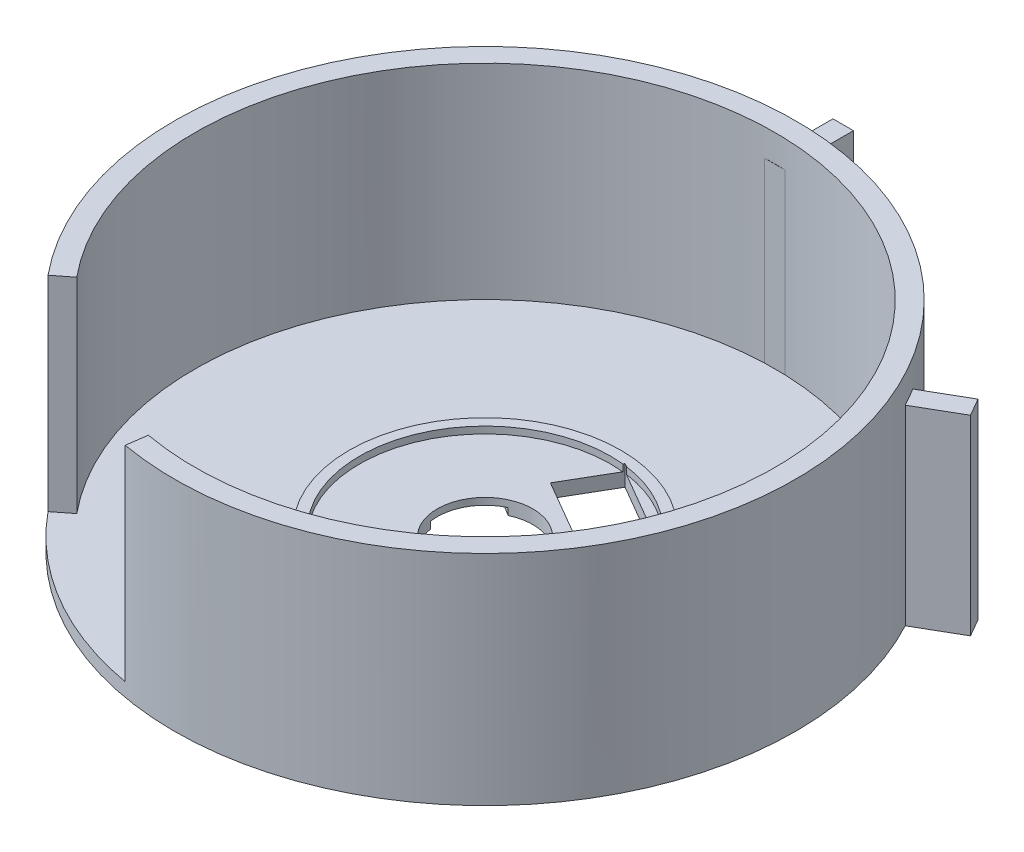
SolidWorks part; units mm, degrees
ref_plane "Front Plane" through (0, 0, 0) normal (0, 0, 1) x (1, 0, 0)
ref_plane "Top Plane" through (0, 0, 0) normal (0, 1, 0) x (1, 0, 0)
ref_plane "Right Plane" through (0, 0, 0) normal (1, 0, 0) x (0, 0, -1)
sketch "Sketch1" plane through (0, 0, 0) normal (0, 1, 0) x (1, 0, 0)
  circle A0 centre (0, 0) radius 45.5
  circle A1 centre (0, 0) radius 42.5
  dimension "D1" = 85
  dimension "D2" = 3
  dimension "D3" = 91
extrude "Boss-Extrude1" add sketch "Sketch1" along normal blind 32
sketch "Sketch2" plane through (0, 0, 0) normal (0, -1, 0) x (1, 0, 0)
  circle A0 centre (0, 0) radius 45.5
extrude "Boss-Extrude2" add sketch "Sketch2" against normal blind 2
sketch "Sketch3" plane through (0, 2, 0) normal (0, 1, 0) x (1, 0, 0)
  circle A0 centre (0, 0) radius 7
  dimension "D1" = 14
extrude "Cut-Extrude1" cut sketch "Sketch3" against normal blind 2
sketch "Sketch7" plane through (0, 2, 0) normal (0, 1, 0) x (1, 0, 0)
  line L12 (1.5, 52.4735) -> (1.5, 42.4735)
  line L13 (1.5, 52.4735) -> (-1.5, 52.4735)
  line L14 (-1.5, 52.4735) -> (-1.5, 42.4735)
  line L16 (46.1934, 24.9377) -> (37.5331, 19.9377)
  line L17 (46.1934, 24.9377) -> (44.6934, 27.5358)
  line L18 (44.6934, 27.5358) -> (36.0331, 22.5358)
  line L32 (-1.5, 42.4735) -> (1.5, 42.4735)
  line L37 (36.0331, 22.5358) -> (37.5331, 19.9377)
  circle A0 centre (0, 0) radius 42.5 construction
  point P27 (0, 0)
  dimension "D1" = 3
  dimension "D2" = 3
  dimension "D3" = 10
  dimension "D4" = 10
  dimension "D5" = 10
extrude "Boss-Extrude4" add sketch "Sketch7" along normal blind 26 and the other way blind 2
sketch "Sketch8" plane through (0, 2, 0) normal (0, 1, 0) x (1, 0, 0)
  circle A0 centre (0, 0) radius 19.8902
  circle A1 centre (0, 0) radius 18.3902
  dimension "D1" = 1.5
extrude "Boss-Extrude5" add sketch "Sketch8" along normal blind 1
sketch "Sketch10" plane through (0, 0, 0) normal (0, -1, 0) x (1, 0, 0)
  line L0 (0, -52.4735) -> (0, 8.0171) construction
  line L5 (1.5, -52.4735) -> (-1.5, -52.4735) construction
  line L8 (46.1934, -24.9377) -> (44.6934, -27.5358) construction
  line L24 (12.911, -7.4542) -> (45.4434, -26.2368) construction
  line L25 (2.0167, -18.4947) -> (14.9819, -10.9512)
  line L26 (2.0167, -18.4947) -> (-2.0065, -11.5799)
  line L27 (14.9819, -10.9512) -> (10.9587, -4.0365)
  line L28 (-2.0065, -11.5799) -> (10.9587, -4.0365)
  dimension "D1" = 15
  dimension "D2" = 8
  dimension "D3" = 9
extrude "Cut-Extrude4" cut sketch "Sketch10" against normal blind 5.5
sketch "Sketch11" plane through (0, 2, 0) normal (0, 1, 0) x (1, 0, 0)
  line L0 (0, 0) -> (-22.75, -39.4042) construction
  line L1 (-32.6066, -26.8741) -> (-35.1652, -28.8731)
  line L2 (-7.4952, -41.7388) -> (-7.926, -44.8043)
  line L5 (-35.1652, -28.8731) -> (-33.825, -37.7542)
  line L6 (-33.825, -37.7542) -> (-11.7383, -48.7724)
  line L7 (-11.7383, -48.7724) -> (-7.926, -44.8043)
  line L8 (-32.6066, -26.8741) -> (-25.9653, -26.8741)
  line L9 (-25.9653, -26.8741) -> (-9.9785, -35.4192)
  line L10 (-9.9785, -35.4192) -> (-7.4952, -41.7388)
  circle A0 centre (0, 0) radius 45.5 construction
  dimension "D1" = 22
  dimension "D2" = 22
extrude "Cut-Extrude5" cut sketch "Sketch11" along normal blind 58.5
sketch "Sketch12" plane through (0, 0, 0) normal (0, -1, 0) x (1, 0, 0)
  line L0 (-6.9123, 1.1048) -> (-24.2076, -9.4803)
  line L1 (-6.9123, 1.1048) -> (-2.5191, -6.0733)
  line L2 (-24.2076, -9.4803) -> (-19.8145, -16.6584)
  line L3 (-2.5191, -6.0733) -> (-19.8145, -16.6584)
  circle A0 centre (0, 0) radius 7 construction
extrude "Cut-Extrude6" cut sketch "Sketch12" against normal blind 1
ref_plane "Plane1" through (22.8819, 0, -39.3277) normal (0.5029, 0, -0.8643) x (-0.8643, 0, -0.5029)
sketch "Sketch13" plane through (22.8819, 0, -39.3277) normal (0.5029, 0, -0.8643) x (-0.8643, 0, -0.5029)
  line L0 (45.5, 32) -> (-45.5, 32) construction
  line L1 (-1.3794, 32) -> (1.0206, 32)
  line L2 (-1.3794, 32) -> (-1.3794, 28)
  line L3 (-1.3794, 28) -> (1.0206, 28)
  line L4 (1.0206, 32) -> (1.0206, 28)
  dimension "D1" = 2.4
  dimension "D2" = 4
